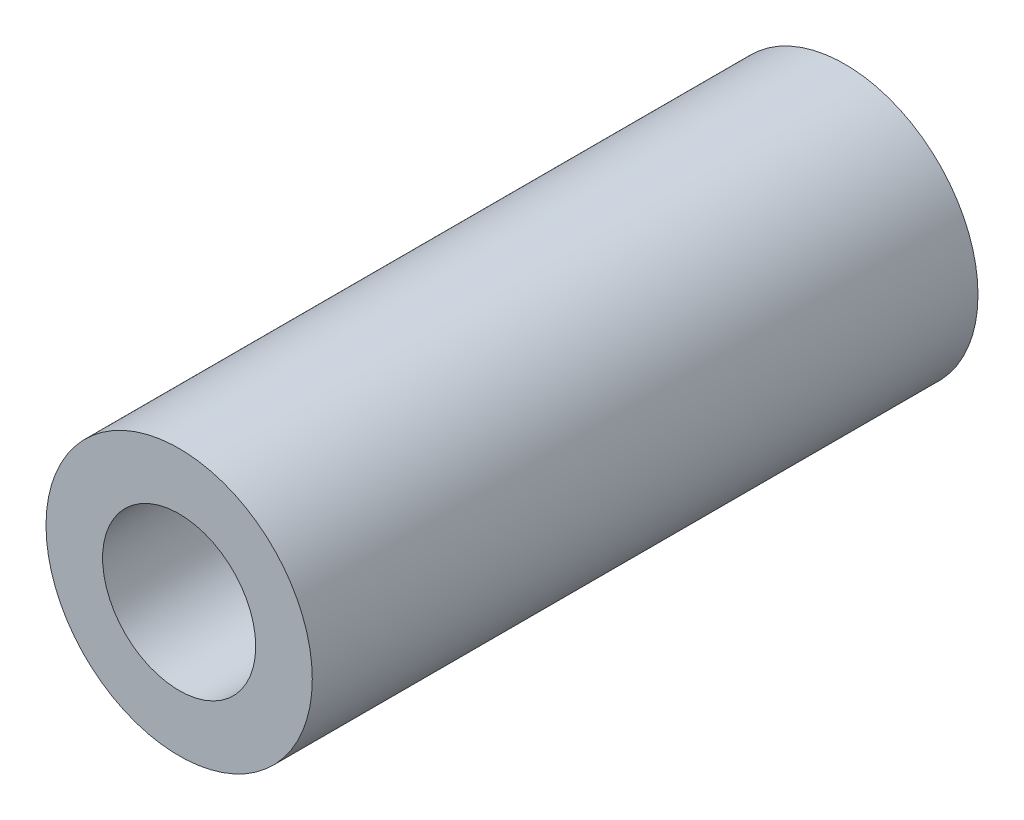
SolidWorks part; units mm, degrees
ref_plane "Front Plane" through (0, 0, 0) normal (0, 0, 1) x (1, 0, 0)
ref_plane "Top Plane" through (0, 0, 0) normal (0, 1, 0) x (1, 0, 0)
ref_plane "Right Plane" through (0, 0, 0) normal (1, 0, 0) x (0, 0, -1)
sketch "Sketch9" plane through (0, 0, 0) normal (0, 0, 1) x (1, 0, 0)
  circle A0 centre (-11.9027, 30.0594) radius 2
  dimension "D1" = 4
extrude "Boss-Extrude3" add sketch "Sketch9" along normal blind 10 contours A0
sketch "Sketch12" plane through (0, 0, 10) normal (0, 0, 1) x (1, 0, 0)
  circle A0 centre (-11.9027, 30.0594) radius 1.15
  dimension "D1" = 2.3
extrude "Cut-Extrude2" cut sketch "Sketch12" against normal through all contours A0
